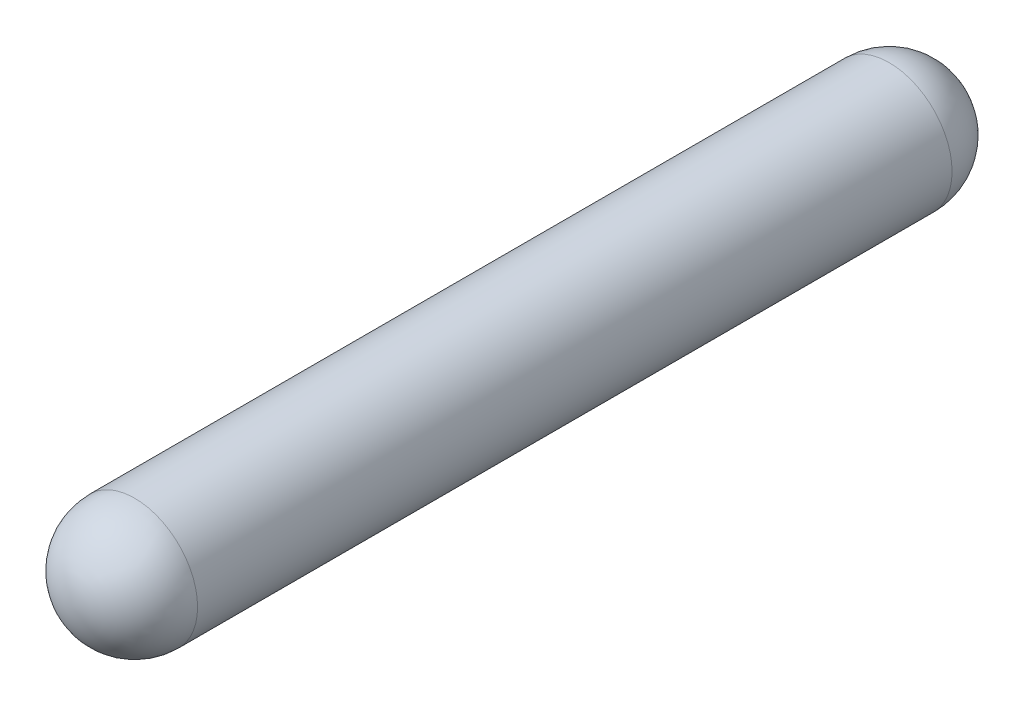
SolidWorks part; units mm, degrees
ref_plane "Front Plane" through (0, 0, 0) normal (0, 0, 1) x (1, 0, 0)
ref_plane "Top Plane" through (0, 0, 0) normal (0, 1, 0) x (1, 0, 0)
ref_plane "Right Plane" through (0, 0, 0) normal (1, 0, 0) x (0, 0, -1)
sketch "Sketch1" plane through (0, 0, 0) normal (0, 1, 0) x (1, 0, 0)
  line L0 (0, 0) -> (0, 35)
  line L1 (-5, 30) -> (-5, 0)
  line L2 (-5, 0) -> (0, 0)
  arc A0 (0, 35) -> (-5, 30) centre (0, 30) ccw
  point P4 (0, 0)
  dimension "D1" = 30
  dimension "D2" = 5
revolve "Revolve1" add sketch "Sketch1" angle 360 about L0
mirror "Mirror1" about plane through (0, 0, 0) normal (0, 0, 1) of "Revolve1"
